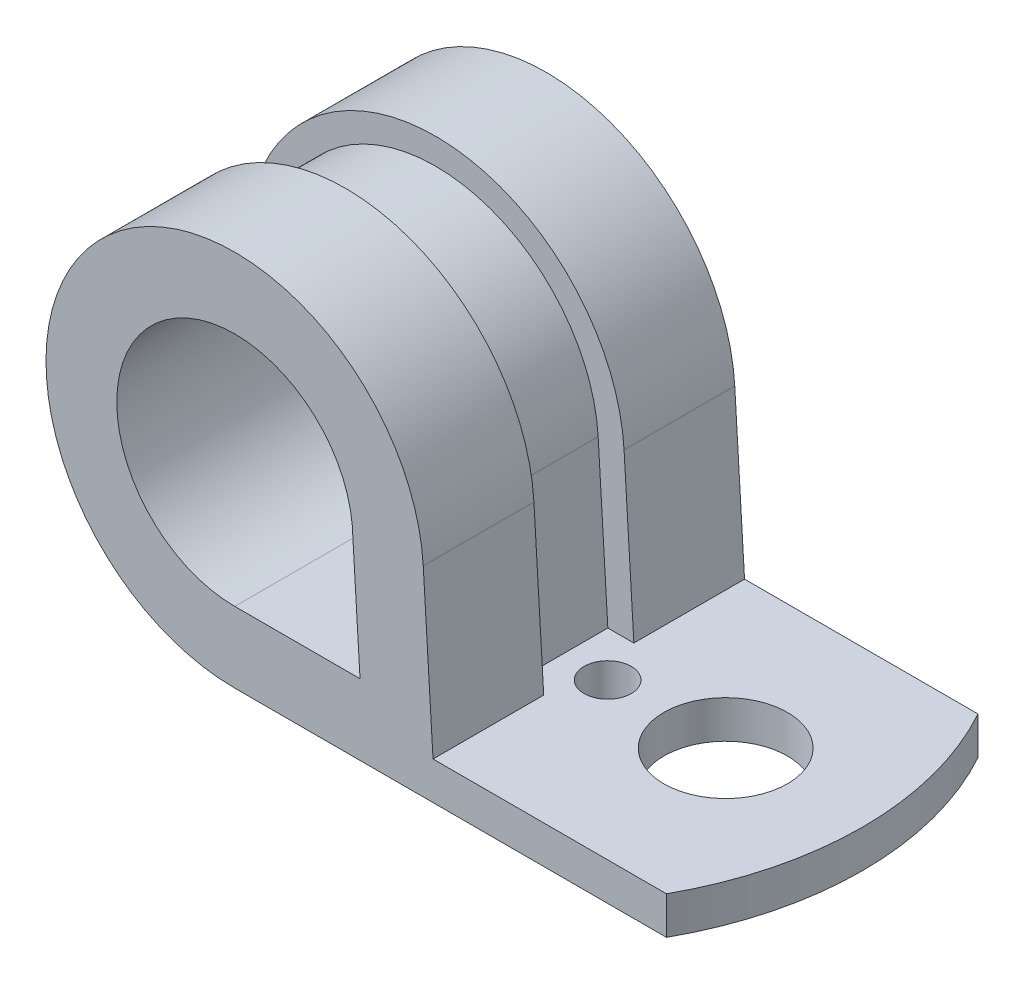
SolidWorks part; units mm, degrees
ref_plane "Center plane" through (0, 0, 0) normal (0, 0, 1) x (1, 0, 0)
ref_plane "Top Plane" through (0, 0, 0) normal (0, 1, 0) x (1, 0, 0)
ref_plane "Right Plane" through (0, 0, 0) normal (1, 0, 0) x (0, 0, -1)
sketch "Sketch1" plane through (0, 0, 0) normal (0, 0, 1) x (1, 0, 0)
  line L0 (0, 0) -> (-25.4, 0)
  line L1 (-25.4, 0) -> (-25.4, 10.16) construction
  line L2 (-15.2584, 10.7709) -> (-14.732, 2.032)
  line L3 (-14.732, 2.032) -> (0, 2.032)
  line L4 (0, 2.032) -> (0, 0)
  line L5 (-15.2584, 10.7709) -> (-19.0795, 10.7709) construction
  line L6 (-19.0795, 10.7709) -> (-18.5531, 2.032) construction
  line L7 (-18.5531, 2.032) -> (-14.732, 2.032) construction
  line L8 (-25.4, 3.81) -> (-18.6602, 3.81)
  line L9 (-19.0795, 10.7709) -> (-18.6602, 3.81)
  arc A0 (-15.2584, 10.7709) -> (-25.4, 0) centre (-25.4, 10.16) ccw
  arc A1 (-19.0795, 10.7709) -> (-25.4, 3.81) centre (-25.4, 10.16) ccw
  point P3 (-35.56, 10.16)
  dimension "D1" = 12.7
  dimension "D2" = 3.81
  dimension "D3" = 14.732
  dimension "D4" = 35.56
  dimension "D5" = 2.032
extrude "Boss-Extrude1" add sketch "Sketch1" along normal mid plane 16.764
sketch "Sketch3" plane through (0, 2.032, 0) normal (0, 1, 0) x (1, 0, 0)
  line L0 (0, 0) -> (-17.2867, 0) construction
  line L1 (0, 8.382) -> (-14.732, 8.382) construction
  line L2 (0, -8.382) -> (-14.732, -8.382) construction
  line L3 (0, 8.382) -> (-2.1681, 8.382)
  line L4 (0, -8.382) -> (-2.1681, -8.382)
  line L5 (0, 8.382) -> (0, -8.382)
  arc A0 (-2.1681, -8.382) -> (-2.1681, 8.382) centre (-17.2867, 0) ccw
  line M1 (0, 8.382) -> (-14.732, 8.382)
  line M3 (-14.732, -8.382) -> (0, -8.382)
  line M4 (0, -8.382) -> (0, 8.382)
extrude "Cut-Extrude2" cut sketch "Sketch3" against normal up to vertex (2.032 mm away) contours A0 M3 M4 | A0 L5 M1 up to point (0, 0, 8.382)
sketch "Sketch4" plane through (0, 2.032, 0) normal (0, 1, 0) x (1, 0, 0)
  line L0 (0, 0) -> (-14.732, 0) construction
  line L1 (-14.732, -8.382) -> (-14.732, 8.382) construction
  line L2 (-7.366, 3.3274) -> (-7.366, 6.35) construction
  circle A0 centre (-7.366, 0) radius 3.3274
  circle A1 centre (-13.716, 0) radius 1.27
  dimension "D1" = 6.6548
  dimension "D2" = 2.54
  dimension "D3" = 6.35
extrude "Cut-Extrude3" cut sketch "Sketch4" against normal through all
sketch "Sketch5" plane through (0, 0, 0) normal (0, 0, 1) x (1, 0, 0)
  line L0 (-25.4, 0) -> (-2.1681, 0) construction
  line L1 (-14.732, 2.032) -> (-15.2584, 10.7709) construction
  line L2 (-25.4, 0) -> (-18.4307, 0)
  line L3 (-14.732, 2.032) -> (-15.2584, 10.7709)
  line L4 (-16.1315, 2.032) -> (-16.6529, 10.6869)
  line L5 (-25.4, 1.397) -> (-18.5148, 1.397)
  line L6 (-16.1265, 1.948) -> (-16.6529, 10.6869) construction
  line L7 (-25.4, 1.397) -> (-2.1681, 1.397) construction
  line L8 (-14.732, 2.032) -> (-15.2584, 10.7709) construction
  line L9 (-25.4, 0) -> (-2.1681, 0) construction
  line L10 (-14.732, 2.032) -> (-16.1315, 2.032)
  line L11 (-18.5148, 1.397) -> (-18.4307, 0)
  line L12 (-18.6602, 3.81) -> (-19.0795, 10.7709) construction
  arc A0 (-15.2584, 10.7709) -> (-25.4, 0) centre (-25.4, 10.16) ccw construction
  arc A1 (-15.2584, 10.7709) -> (-25.4, 0) centre (-25.4, 10.16) ccw
  arc A2 (-16.6529, 10.6869) -> (-25.4, 1.397) centre (-25.4, 10.16) ccw
  dimension "D1" = 1.397
extrude "Cut-Extrude4" cut sketch "Sketch5" against normal mid plane 4.8514
ref_plane "Lock plane" through (-25.4, 0, 0) normal (1, 0, 0) x (0, 0, -1)
